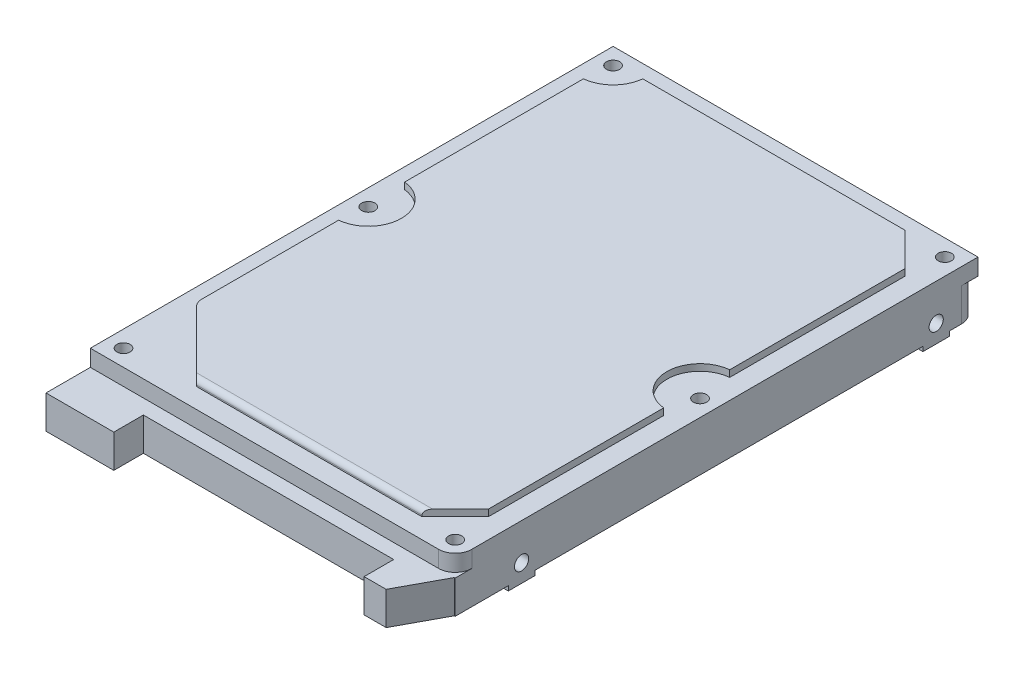
SolidWorks part; units mm, degrees
ref_plane "Front Plane" through (0, 0, 0) normal (0, 0, 1) x (1, 0, 0)
ref_plane "Top Plane" through (0, 0, 0) normal (0, 1, 0) x (1, 0, 0)
ref_plane "Right Plane" through (0, 0, 0) normal (1, 0, 0) x (0, 0, -1)
ref_plane "Plane1" through (0, 0, 0) normal (0, 1, 0) x (1, 0, 0)
sketch "S2D0001" plane through (0, 0, 0) normal (0, 1, 0) x (1, 0, 0)
  line L0 (0, 0) -> (69.85, 0)
  line L1 (69.85, 0) -> (69.85, 100.076)
  line L2 (69.85, 100.076) -> (0, 100.076)
  line L3 (0, 100.076) -> (0, 0)
extrude "Boss-Extrude1" add sketch "S2D0001" against normal blind 3.175
fillet "Fillet1" radius 3.175 1 edges at (69.85, -1.5875, 0)
ref_plane "Plane2" through (0, 0, 0) normal (0, 1, 0) x (1, 0, 0)
sketch "S2D0002" plane through (0, 0, 0) normal (0, 1, 0) x (1, 0, 0)
  circle A0 centre (3.175, 96.901) radius 1.27
  circle A1 centre (66.675, 96.901) radius 1.27
  circle A2 centre (3.175, 50.038) radius 1.27
  circle A3 centre (66.675, 50.038) radius 1.27
  circle A4 centre (3.175, 3.175) radius 1.27
  circle A5 centre (66.675, 3.175) radius 1.27
  dimension "D1" = 2.54
extrude "Cut-Extrude1" cut sketch "S2D0002" against normal blind 3.4925
sketch "Sketch3" plane through (0, 0, 0) normal (0, 1, 0) x (-1, 0, 0)
  line L0 (-9.4932, -96.266) -> (-59.69, -96.266)
  line L1 (-66.04, -89.916) -> (-66.04, -56.3562)
  line L2 (-66.04, -43.7198) -> (-66.04, -10.16)
  line L3 (-59.69, -3.81) -> (-16.51, -3.81)
  line L4 (-3.81, -16.51) -> (-3.81, -43.7198)
  line L5 (-3.81, -56.3562) -> (-3.81, -90.5828)
  line L6 (-3.81, -16.51) -> (-16.51, -3.81)
  line L7 (-66.04, -10.16) -> (-59.69, -3.81)
  line L8 (-59.69, -96.266) -> (-66.04, -89.916)
  arc A0 (-66.04, -56.3562) -> (-66.04, -43.7198) centre (-66.675, -50.038) ccw
  arc A1 (-3.81, -90.5828) -> (-9.4932, -96.266) centre (-3.175, -96.901) ccw
  arc A2 (-3.81, -43.7198) -> (-3.81, -56.3562) centre (-3.175, -50.038) ccw
  dimension "D1" = 6.35
extrude "Boss-Extrude2" add sketch "Sketch3" along normal blind 1.27
fillet "Fillet2" radius 2.54 1 edges at (3.81, 0.635, -16.51)
fillet "Fillet3" radius 1.016 1 edges at (38.1, 1.27, -3.81)
sketch "Sketch4" plane through (0, -3.175, 0) normal (0, -1, 0) x (1, 0, 0)
  line L0 (0, -96.901) -> (0, 0)
  line L1 (66.675, -100.076) -> (3.175, -100.076)
  line L2 (69.85, 0) -> (69.85, -96.901)
  line L3 (0, 0) -> (69.85, 0)
  arc A0 (0, -96.901) -> (3.175, -100.076) centre (3.175, -96.901) ccw
  arc A1 (66.675, -100.076) -> (69.85, -96.901) centre (66.675, -96.901) ccw
extrude "Boss-Extrude3" add sketch "Sketch4" along normal blind 6.35
ref_plane "Plane3" through (0, 0, 0) normal (1, 0, 0) x (0, 0, -1)
sketch "S2D0005" plane through (0, 0, 0) normal (1, 0, 0) x (0, 0, -1)
  line L0 (10.16, -3.175) -> (15.24, -3.175)
  line L1 (15.24, -3.175) -> (15.24, -9.525)
  line L2 (15.24, -9.525) -> (10.16, -9.525)
  line L3 (10.16, -9.525) -> (10.16, -3.175)
  line L4 (89.535, -3.175) -> (94.615, -3.175)
  line L5 (94.615, -3.175) -> (94.615, -9.525)
  line L6 (94.615, -9.525) -> (89.535, -9.525)
  line L7 (89.535, -9.525) -> (89.535, -3.175)
  point P8 (12.7, -9.525)
  point P9 (92.075, -9.525)
  point P10 (12.7, -6.985)
  point P11 (92.075, -6.985)
extrude "Boss-Extrude4" add sketch "S2D0005" along normal up to surface (69.85 mm away) up to face at (69.85, -4.1672, -50.038)
ref_plane "Plane4" through (12.7, -5.6261, -92.075) normal (0, 0, 1) x (0, 1, 0)
sketch "S2D0007" plane through (12.7, -5.6261, -92.075) normal (0, 0, 1) x (0, 1, 0)
  line L0 (-1.3589, -0.8165) -> (0, 0)
  line L1 (-1.3589, -0.8165) -> (-2.7178, 0)
  line L2 (0, 0) -> (0, 12.7)
  line L3 (-2.7178, 0) -> (-2.7178, 12.7)
  line L4 (0, 12.7) -> (-1.3589, 12.7)
  line L5 (-2.7178, 12.7) -> (-1.3589, 12.7)
  line L6 (-1.3589, -1.4923) -> (-1.3589, 13.3758) construction
revolve "Cut-Revolve1" cut sketch "S2D0007" angle 360 about L6
ref_plane "Plane5" through (12.7, -5.6261, -12.7) normal (0, 0, 1) x (0, 1, 0)
sketch "Sketch7" plane through (12.7, -5.6261, -12.7) normal (0, 0, 1) x (0, 1, 0)
  line L0 (-1.3589, -0.8165) -> (0, 0)
  line L1 (-1.3589, -0.8165) -> (-2.7178, 0)
  line L2 (0, 0) -> (0, 12.7)
  line L3 (-2.7178, 0) -> (-2.7178, 12.7)
  line L4 (0, 12.7) -> (-1.3589, 12.7)
  line L5 (-2.7178, 12.7) -> (-1.3589, 12.7)
  line L6 (-1.3589, -1.4923) -> (-1.3589, 13.3758) construction
revolve "Cut-Revolve2" cut sketch "Sketch7" angle 360 about L6
ref_plane "Plane6" through (57.15, -8.3439, -12.7) normal (0, 0, 1) x (0, -1, 0)
sketch "S2D0008" plane through (57.15, -8.3439, -12.7) normal (0, 0, 1) x (0, -1, 0)
  line L0 (-1.3589, -0.8165) -> (0, 0)
  line L1 (-1.3589, -0.8165) -> (-2.7178, 0)
  line L2 (0, 0) -> (0, 12.7)
  line L3 (-2.7178, 0) -> (-2.7178, 12.7)
  line L4 (0, 12.7) -> (-1.3589, 12.7)
  line L5 (-2.7178, 12.7) -> (-1.3589, 12.7)
  line L6 (-1.3589, -1.4923) -> (-1.3589, 13.3758) construction
revolve "Cut-Revolve3" cut sketch "S2D0008" angle 360 about L6
ref_plane "Plane7" through (57.15, -8.3439, -92.075) normal (0, 0, 1) x (0, -1, 0)
sketch "S2D0009" plane through (57.15, -8.3439, -92.075) normal (0, 0, 1) x (0, -1, 0)
  line L0 (-1.3589, -0.8165) -> (0, 0)
  line L1 (-1.3589, -0.8165) -> (-2.7178, 0)
  line L2 (0, 0) -> (0, 12.7)
  line L3 (-2.7178, 0) -> (-2.7178, 12.7)
  line L4 (0, 12.7) -> (-1.3589, 12.7)
  line L5 (-2.7178, 12.7) -> (-1.3589, 12.7)
  line L6 (-1.3589, -1.4923) -> (-1.3589, 13.3758) construction
revolve "Cut-Revolve4" cut sketch "S2D0009" angle 360 about L6
sketch "Sketch10" plane through (0, -9.525, 0) normal (0, -1, 0) x (1, 0, 0)
  line L0 (0, -94.615) -> (0, -89.535)
  line L1 (0, -89.535) -> (6.35, -89.535)
  line L2 (6.35, -94.615) -> (0, -94.615)
  line L3 (0, -15.24) -> (0, -10.16)
  line L4 (0, -10.16) -> (6.35, -10.16)
  line L5 (6.35, -15.24) -> (0, -15.24)
  line L6 (69.85, -10.16) -> (69.85, -15.24)
  line L7 (69.85, -15.24) -> (63.5, -15.24)
  line L8 (63.5, -10.16) -> (69.85, -10.16)
  line L9 (69.85, -89.535) -> (69.85, -94.615)
  line L10 (69.85, -94.615) -> (63.5, -94.615)
  line L11 (63.5, -89.535) -> (69.85, -89.535)
  arc A0 (63.5, -10.16) -> (63.5, -15.24) centre (63.5, -12.7) ccw
  arc A1 (6.35, -15.24) -> (6.35, -10.16) centre (6.35, -12.7) ccw
  arc A2 (6.35, -94.615) -> (6.35, -89.535) centre (6.35, -92.075) ccw
  arc A3 (63.5, -89.535) -> (63.5, -94.615) centre (63.5, -92.075) ccw
  point P20 (6.35, -92.075)
  point P21 (6.35, -12.7)
  point P22 (63.5, -12.7)
  point P23 (63.5, -92.075)
extrude "Boss-Extrude5" add sketch "Sketch10" along normal blind 0.889
ref_plane "Plane8" through (4.9911, -4.064, -92.075) normal (0, 0, 1) x (-1, 0, 0)
sketch "S2D0019" plane through (4.9911, -4.064, -92.075) normal (0, 0, 1) x (-1, 0, 0)
  line L0 (-1.3589, -0.8165) -> (0, 0)
  line L1 (-1.3589, -0.8165) -> (-2.7178, 0)
  line L2 (0, 0) -> (0, 6.35)
  line L3 (-2.7178, 0) -> (-2.7178, 6.35)
  line L4 (0, 6.35) -> (-1.3589, 6.35)
  line L5 (-2.7178, 6.35) -> (-1.3589, 6.35)
  line L6 (-1.3589, -1.1748) -> (-1.3589, 6.7083) construction
revolve "Cut-Revolve5" cut sketch "S2D0019" angle 360 about L6
ref_plane "Plane9" through (62.1411, -4.064, -92.075) normal (0, 0, 1) x (-1, 0, 0)
sketch "Sketch12" plane through (62.1411, -4.064, -92.075) normal (0, 0, 1) x (-1, 0, 0)
  line L0 (-1.3589, -0.8165) -> (0, 0)
  line L1 (-1.3589, -0.8165) -> (-2.7178, 0)
  line L2 (0, 0) -> (0, 6.35)
  line L3 (-2.7178, 0) -> (-2.7178, 6.35)
  line L4 (0, 6.35) -> (-1.3589, 6.35)
  line L5 (-2.7178, 6.35) -> (-1.3589, 6.35)
  line L6 (-1.3589, -1.1748) -> (-1.3589, 6.7083) construction
revolve "Cut-Revolve6" cut sketch "Sketch12" angle 360 about L6
ref_plane "Plane10" through (62.1411, -4.064, -12.7) normal (0, 0, 1) x (-1, 0, 0)
sketch "S2D0021" plane through (62.1411, -4.064, -12.7) normal (0, 0, 1) x (-1, 0, 0)
  line L0 (-1.3589, -0.8165) -> (0, 0)
  line L1 (-1.3589, -0.8165) -> (-2.7178, 0)
  line L2 (0, 0) -> (0, 6.35)
  line L3 (-2.7178, 0) -> (-2.7178, 6.35)
  line L4 (0, 6.35) -> (-1.3589, 6.35)
  line L5 (-2.7178, 6.35) -> (-1.3589, 6.35)
  line L6 (-1.3589, -1.1748) -> (-1.3589, 6.7083) construction
revolve "Cut-Revolve7" cut sketch "S2D0021" angle 360 about L6
ref_plane "Plane11" through (4.9911, -4.064, -12.7) normal (0, 0, 1) x (-1, 0, 0)
sketch "Sketch14" plane through (4.9911, -4.064, -12.7) normal (0, 0, 1) x (-1, 0, 0)
  line L0 (-1.3589, -0.8165) -> (0, 0)
  line L1 (-1.3589, -0.8165) -> (-2.7178, 0)
  line L2 (0, 0) -> (0, 6.35)
  line L3 (-2.7178, 0) -> (-2.7178, 6.35)
  line L4 (0, 6.35) -> (-1.3589, 6.35)
  line L5 (-2.7178, 6.35) -> (-1.3589, 6.35)
  line L6 (-1.3589, -1.1748) -> (-1.3589, 6.7083) construction
revolve "Cut-Revolve8" cut sketch "Sketch14" angle 360 about L6
sketch "Sketch15" plane through (0, -9.525, 0) normal (0, -1, 0) x (1, 0, 0)
  line L0 (69.6836, 0) -> (65.1116, 8.4836)
  line L1 (65.1116, 8.4836) -> (60.8952, 8.4836)
  line L2 (60.8952, 8.4836) -> (60.8952, 2.8194)
  line L3 (60.8952, 2.8194) -> (12.9794, 2.8194)
  line L4 (12.9794, 2.8194) -> (12.9794, 8.4836)
  line L5 (12.9794, 8.4836) -> (0, 8.4836)
  line L6 (0, 8.4836) -> (0, 0)
  line L7 (0, 0) -> (69.6836, 0)
  dimension "D1" = 5.6642
ref_plane "Plane12" through (0, -3.175, 0) normal (0, -1, 0) x (1, 0, 0)
extrude "Boss-Extrude6" add sketch "Sketch15" against normal up to surface (6.35 mm away) up to plane "Plane12"
